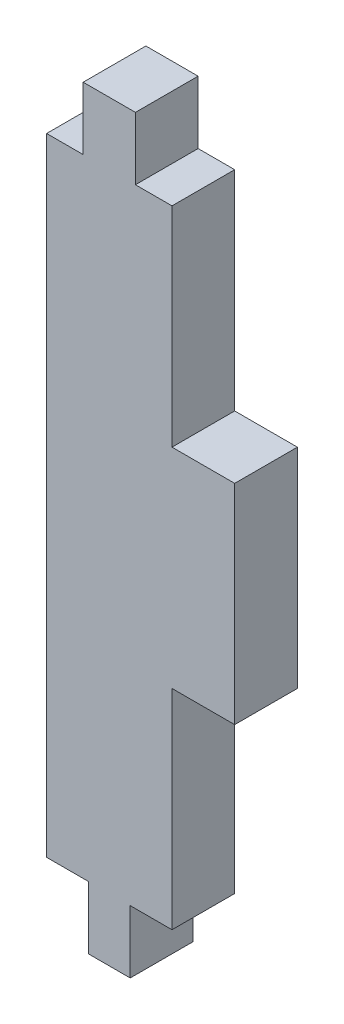
SolidWorks part; units mm, degrees
ref_plane "Front Plane" through (0, 0, 0) normal (0, 0, 1) x (1, 0, 0)
ref_plane "Top Plane" through (0, 0, 0) normal (0, 1, 0) x (1, 0, 0)
ref_plane "Right Plane" through (0, 0, 0) normal (1, 0, 0) x (0, 0, -1)
sketch "Sketch1" plane through (0, 0, 0) normal (0, 0, 1) x (1, 0, 0)
  line L0 (-34.3139, -11.18) -> (-30.1473, -11.18)
  line L1 (-37.2306, -16.18) -> (-27.2306, -16.18)
  line L2 (-37.2306, -16.18) -> (-37.2306, -66.18)
  line L3 (-37.2306, -66.18) -> (-27.2306, -66.18)
  line L4 (-27.2306, -16.18) -> (-27.2306, -66.18)
  line L5 (-37.2306, -16.18) -> (-27.2306, -66.18) construction
  line L6 (-37.2306, -66.18) -> (-27.2306, -16.18) construction
  line L7 (-33.8973, -61.18) -> (-30.5639, -61.18)
  line L8 (-33.8973, -61.18) -> (-33.8973, -71.18)
  line L9 (-33.8973, -71.18) -> (-30.5639, -71.18)
  line L10 (-30.5639, -61.18) -> (-30.5639, -71.18)
  line L11 (-33.8973, -61.18) -> (-30.5639, -71.18) construction
  line L12 (-33.8973, -71.18) -> (-30.5639, -61.18) construction
  line L13 (-34.3139, -11.18) -> (-34.3139, -21.18)
  line L14 (-34.3139, -21.18) -> (-30.1473, -21.18)
  line L15 (-30.1473, -11.18) -> (-30.1473, -21.18)
  line L16 (-34.3139, -11.18) -> (-30.1473, -21.18) construction
  line L17 (-34.3139, -21.18) -> (-30.1473, -11.18) construction
  line L19 (-27.2306, -49.5133) -> (-22.2306, -49.5133)
  line L20 (-27.2306, -49.5133) -> (-27.2306, -32.8467)
  line L21 (-27.2306, -32.8467) -> (-22.2306, -32.8467)
  line L22 (-22.2306, -49.5133) -> (-22.2306, -32.8467)
  point P0 (-32.2306, -41.18)
  point P5 (-32.2306, -66.18)
  point P10 (-32.2306, -16.18)
  dimension "D1" = 50
  dimension "D2" = 10
  dimension "D3" = 5
  dimension "D4" = 1.6667
  dimension "D5" = 16.6667
  dimension "D6" = 16.6667
  dimension "D7" = 5
  dimension "D8" = 5
extrude "Boss-Extrude1" add sketch "Sketch1" along normal blind 5 contours L1 L4 L3 L2 | L13 L14 L15 L0 | L10 L9 L8 L7 | L22 L21 L20 L19
equation "\"mat\"=\"mat@V1.assembly\""
equation "\"D3@Sketch1\"=\"mat\""
equation "\"D4@Sketch1\" = 10/6"
equation "\"D1@Boss-Extrude1\"=\"mat\""
equation "\"D7@Sketch1\" = \"mat\""
equation "\"D8@Sketch1\" = \"mat\""
